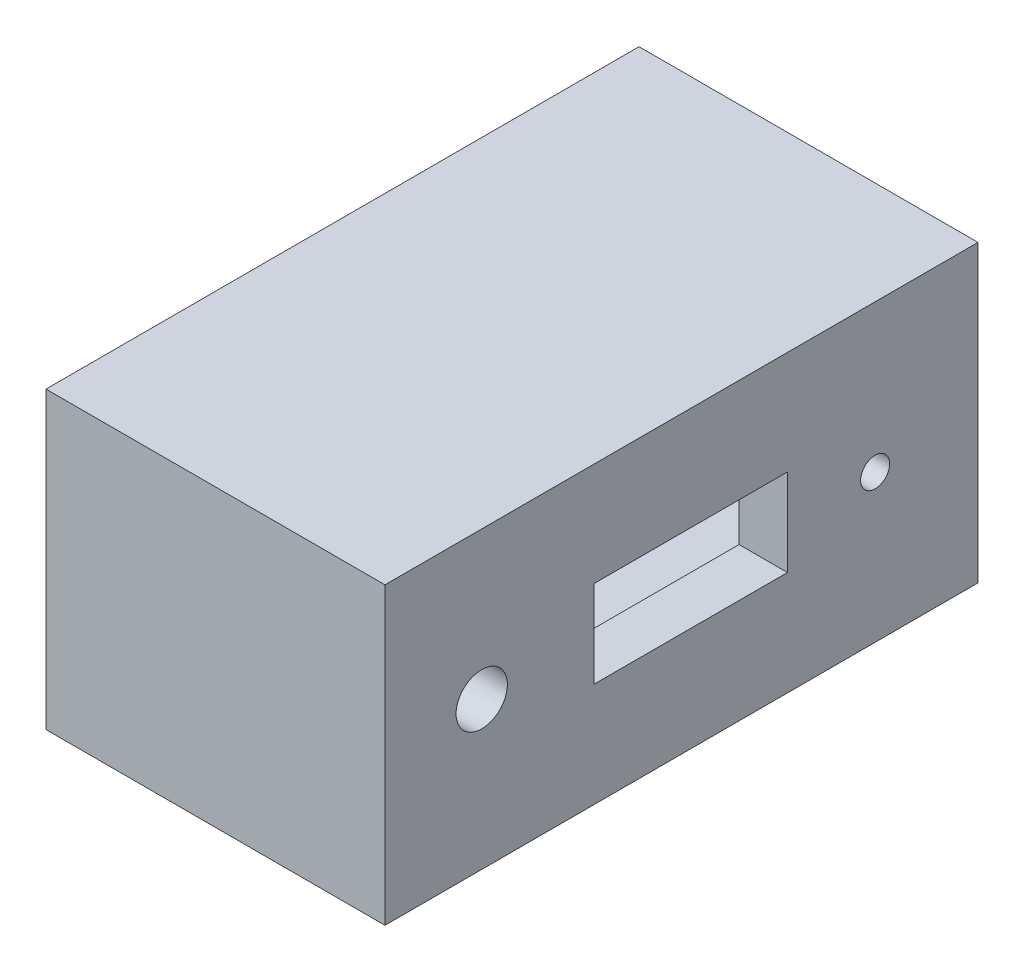
SolidWorks part; units mm, degrees
ref_plane "Front Plane" through (0, 0, 0) normal (0, 0, 1) x (1, 0, 0)
ref_plane "Top Plane" through (0, 0, 0) normal (0, 1, 0) x (1, 0, 0)
ref_plane "Right Plane" through (0, 0, 0) normal (1, 0, 0) x (0, 0, -1)
sketch "Sketch3" plane through (0, 0, 0) normal (1, 0, 0) x (0, 0, -1)
  line L1 (0, 0) -> (6.1233, 0)
  line L2 (0, 0) -> (0, 3.045)
  line L3 (0, 3.045) -> (6.1233, 3.045)
  line L4 (6.1233, 0) -> (6.1233, 3.045)
extrude "Boss-Extrude1" add sketch "Sketch3" along normal blind 3.5
sketch "Sketch4" plane through (0, 0, 0) normal (1, 0, 0) x (0, 0, -1)
  line L1 (0.1108, 2.8972) -> (5.9937, 2.8972)
  line L2 (0.1108, 2.8972) -> (0.1108, 0.1372)
  line L3 (0.1108, 0.1372) -> (5.9937, 0.1372)
  line L4 (5.9937, 2.8972) -> (5.9937, 0.1372)
extrude "Cut-Extrude1" cut sketch "Sketch4" against normal blind 3.5 and the other way blind 3
sketch "Sketch5" plane through (0, 0, 0) normal (1, 0, 0) x (0, 0, -1)
  line L0 (2.156, 1.9767) -> (4.156, 1.9767)
  line L1 (0, 0) -> (1.9984, 0)
  line L2 (0, 0) -> (6.1233, 0) construction
  line L3 (1.9984, 3.045) -> (3.9992, 3.045)
  line L4 (6.1233, 3.045) -> (0, 3.045) construction
  line L5 (2.156, 1.9767) -> (2.156, 1.0767)
  line L6 (2.156, 1.0767) -> (4.156, 1.0767)
  line L8 (4.156, 1.9767) -> (4.156, 1.0767)
  circle A0 centre (0.9992, 1.5225) radius 0.265
  circle A1 centre (5.0612, 1.5225) radius 0.15
  dimension "D1" = 0.3
  dimension "D2" = 0.53
  dimension "D3" = 0.9
  dimension "D4" = 2
extrude "Cut-Extrude4" cut sketch "Sketch5" against normal blind 9.5 and the other way blind 19 contours L8 L0 L5 L6 | A0 | A1
